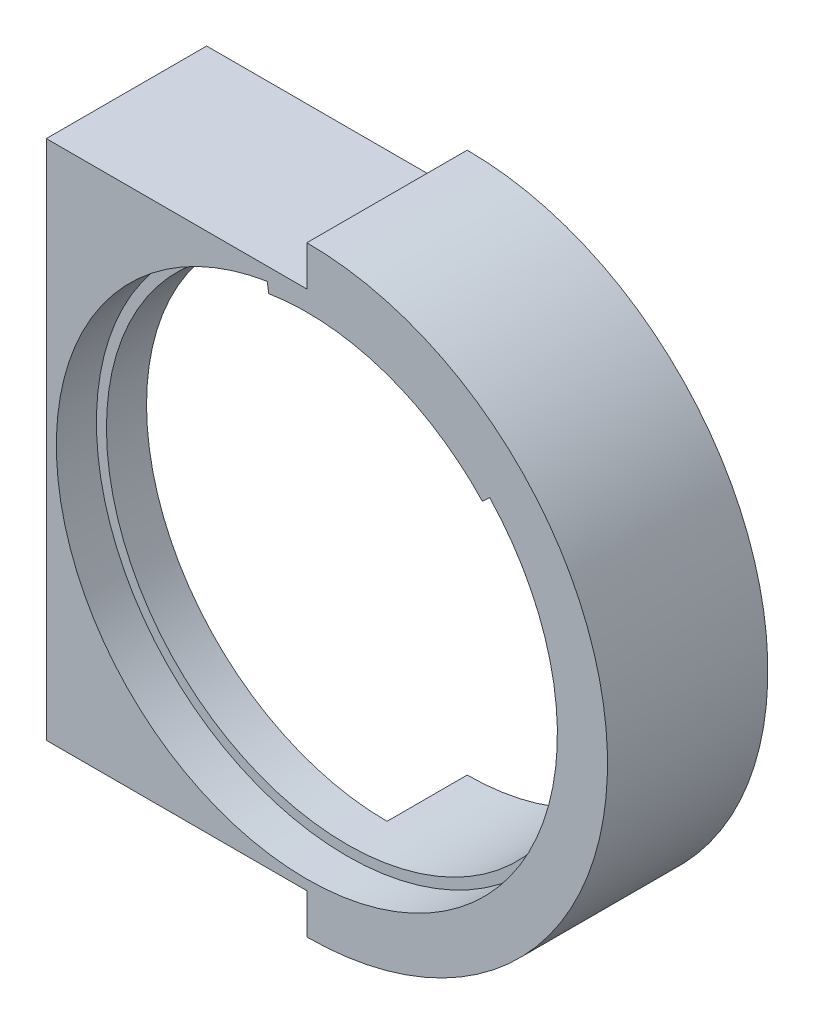
SolidWorks part; units mm, degrees
ref_plane "Front Plane" through (0, 0, 0) normal (0, 0, 1) x (1, 0, 0)
ref_plane "Top Plane" through (0, 0, 0) normal (0, 1, 0) x (1, 0, 0)
ref_plane "Right Plane" through (0, 0, 0) normal (1, 0, 0) x (0, 0, -1)
sketch "Sketch1" plane through (0, 0, 0) normal (0, 0, 1) x (1, 0, 0)
  line L4 (-41.275, -41.275) -> (-41.275, 41.275)
  line L6 (-41.275, 41.275) -> (0, 41.275)
  line L7 (0, 47.625) -> (0, 41.275)
  line L10 (-41.275, -41.275) -> (0, -41.275)
  line L11 (0, -47.625) -> (0, -41.275)
  circle A0 centre (0, 0) radius 38.1
  arc A1 (0, -47.625) -> (0, 47.625) centre (0, 0) ccw
  dimension "D1" = 76.2
  dimension "D2" = 95.25
  dimension "D3" = 6.35
  dimension "D4" = 6.35
extrude "Boss-Extrude1" add sketch "Sketch1" along normal blind 25.4
ref_plane "Plane1" through (0, 0, 12.7) normal (0, 0, -1) x (-1, 0, 0)
sketch "Sketch5" plane through (0, 0, 12.7) normal (0, 0, -1) x (-1, 0, 0)
  line L0 (0.423, -1.1975) -> (-13.9587, 39.5171)
  arc A1 (-13.9587, 39.5171) -> (0.423, -1.1975) centre (-6.7678, 19.1598) ccw
  dimension "D1" = 43.18
revolve "Cut-Revolve3" cut sketch "Sketch5" angle 360 about L0
sketch "Sketch2" plane through (0, 0, 25.4) normal (0, 0, 1) x (1, 0, 0)
  line L0 (-6.2861, 39.1865) -> (0, 0)
  line L1 (0, 0) -> (28.9566, 27.1406)
  arc A0 (-6.2861, 39.1865) -> (28.9566, 27.1406) centre (0, 0) ccw
  point P3 (28.201, 26.4324)
  point P4 (-6.1087, 38.0805)
  dimension "D1" = 79.375
extrude "Cut-Extrude1" cut sketch "Sketch2" against normal blind 6.35
sketch "Sketch4" plane through (0, 0, 0) normal (0, 0, -1) x (-1, 0, 0)
  line L0 (0, 38.1) -> (0, -41.275)
  line L1 (0, -41.275) -> (41.275, -41.275)
  line L2 (41.275, -41.275) -> (41.275, 41.275)
  circle A0 centre (0, 0) radius 38.1 construction
  arc A1 (0, 38.1) -> (41.275, 41.275) centre (2.4641, 275.9421) ccw
  point P0 (0, 38.1)
extrude "Cut-Extrude2" cut sketch "Sketch4" against normal up to surface (12.7 mm away)
